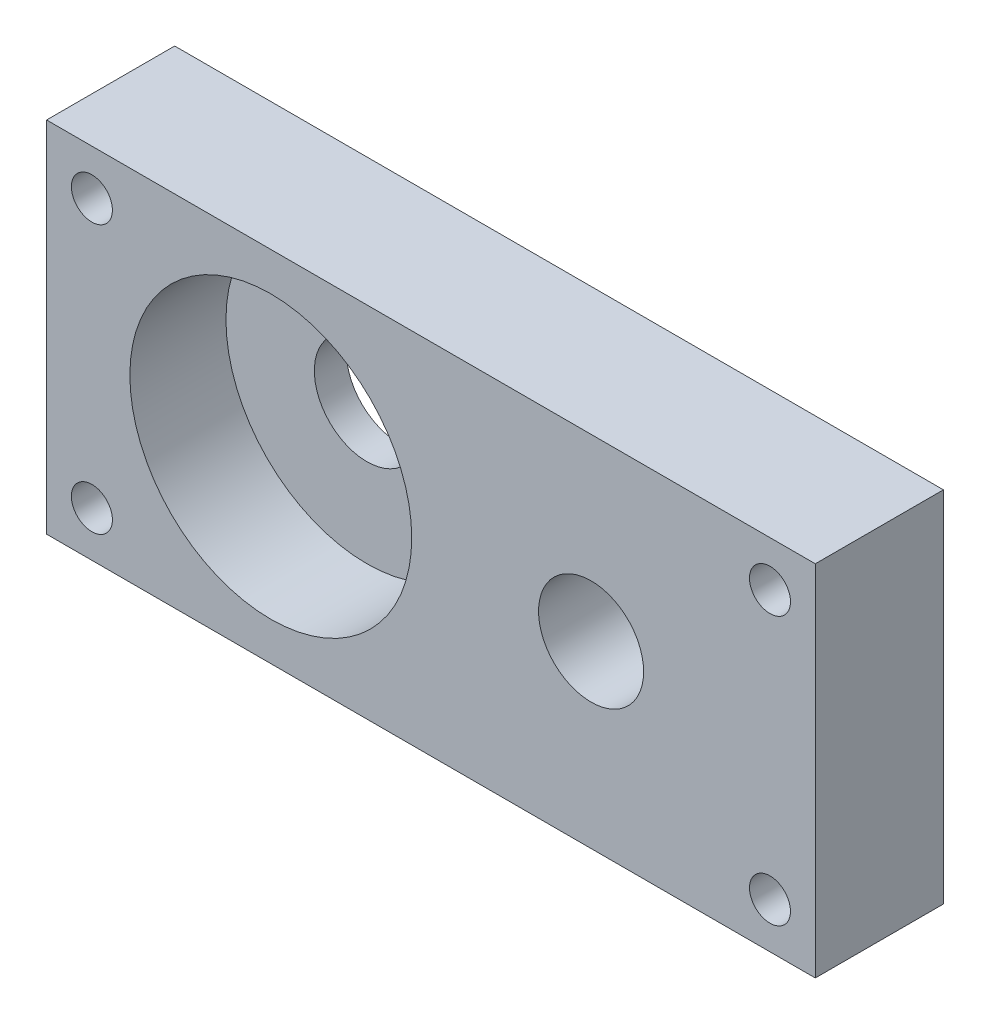
SolidWorks part; units mm, degrees
ref_plane "Front Plane" through (0, 0, 0) normal (0, 0, 1) x (1, 0, 0)
ref_plane "Top Plane" through (0, 0, 0) normal (0, 1, 0) x (1, 0, 0)
ref_plane "Right Plane" through (0, 0, 0) normal (1, 0, 0) x (0, 0, -1)
sketch "Sketch1" plane through (0, 0, 0) normal (0, 0, 1) x (1, 0, 0)
  line L0 (-30, 0) -> (30, 0) construction
  line L1 (30, -14) -> (-30, -14)
  line L2 (30, -14) -> (30, 14)
  line L3 (30, 14) -> (-30, 14)
  line L4 (-30, -14) -> (-30, 14)
  line L5 (30, -14) -> (-30, 14) construction
  line L6 (30, 14) -> (-30, -14) construction
  line L7 (-30, 14) -> (-25.155, 9.155) construction
  line L8 (-30, -14) -> (-23.8174, -7.8174) construction
  line L9 (0, 14) -> (0, 10.472) construction
  circle A0 centre (12.5, 0) radius 4.1
  circle A1 centre (-12.5, 0) radius 4.1
  circle A2 centre (-26.4645, 10.4645) radius 1.6
  circle A3 centre (-26.4645, -10.4645) radius 1.6
  circle A4 centre (26.4645, -10.4645) radius 1.6
  circle A5 centre (26.4645, 10.4645) radius 1.6
  point P0 (0, 0)
  dimension "D3" = 25
  dimension "D4" = 8.2
  dimension "D5" = 8.2
  dimension "D7" = 3.2
  dimension "D8" = 3.2
  dimension "D1" = 28
  dimension "D2" = 60
  dimension "D6" = 12.5
  dimension "D9" = 5
  dimension "D10" = 5
  dimension "D11" = 3.5355
  dimension "D12" = 3.5355
extrude "Boss-Extrude1" add sketch "Sketch1" along normal blind 10
sketch "Sketch2" plane through (0, 0, 10) normal (0, 0, 1) x (1, 0, 0)
  circle A0 centre (-12.5, 0) radius 11
  dimension "D1" = 22
extrude "Cut-Extrude1" cut sketch "Sketch2" against normal blind 7.5
